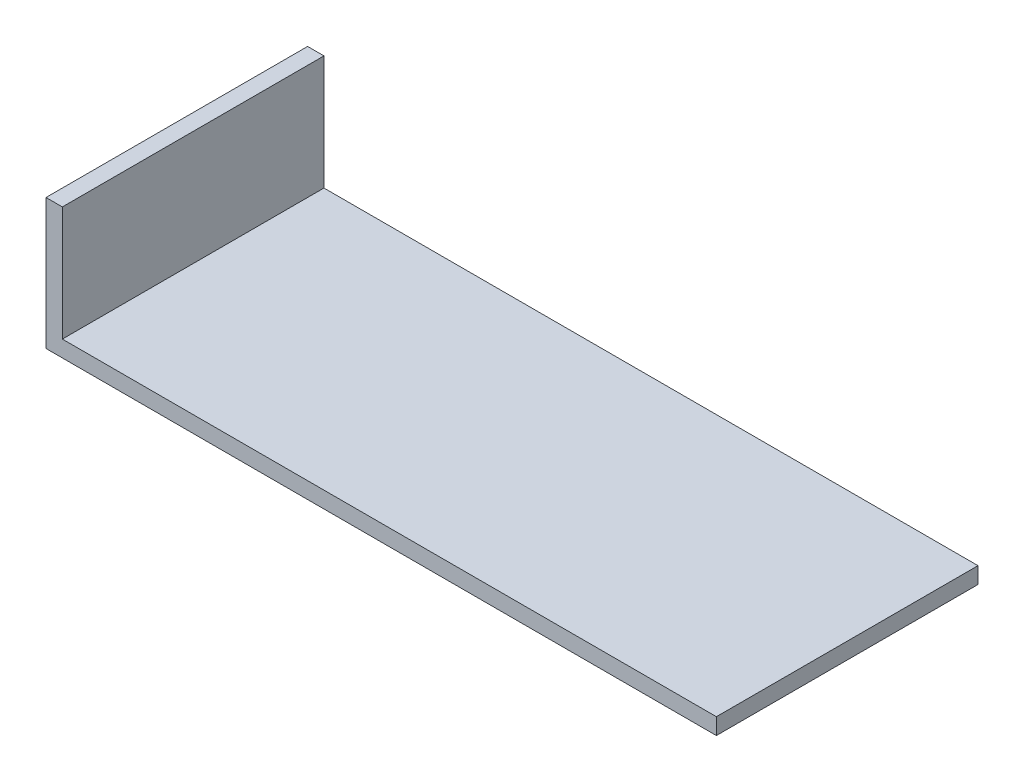
SolidWorks part; units mm, degrees
material "1060 Alloy"
ref_plane "Front Plane" through (0, 0, 0) normal (0, 0, 1) x (1, 0, 0)
ref_plane "Top Plane" through (0, 0, 0) normal (0, 1, 0) x (1, 0, 0)
ref_plane "Right Plane" through (0, 0, 0) normal (1, 0, 0) x (0, 0, -1)
sketch "Sketch1" plane through (0, 0, 0) normal (0, 0, 1) x (1, 0, 0)
  line L0 (0, 0) -> (130.175, 0)
  line L1 (130.175, 0) -> (130.175, 3.175)
  line L2 (130.175, 3.175) -> (3.175, 3.175)
  line L3 (3.175, 3.175) -> (3.175, 25.4)
  line L4 (3.175, 25.4) -> (0, 25.4)
  line L5 (0, 25.4) -> (0, 0)
  dimension "D1" = 3.175
  dimension "D2" = 130.175
  dimension "D3" = 25.4
extrude "Boss-Extrude1" add sketch "Sketch1" along normal blind 50.8
